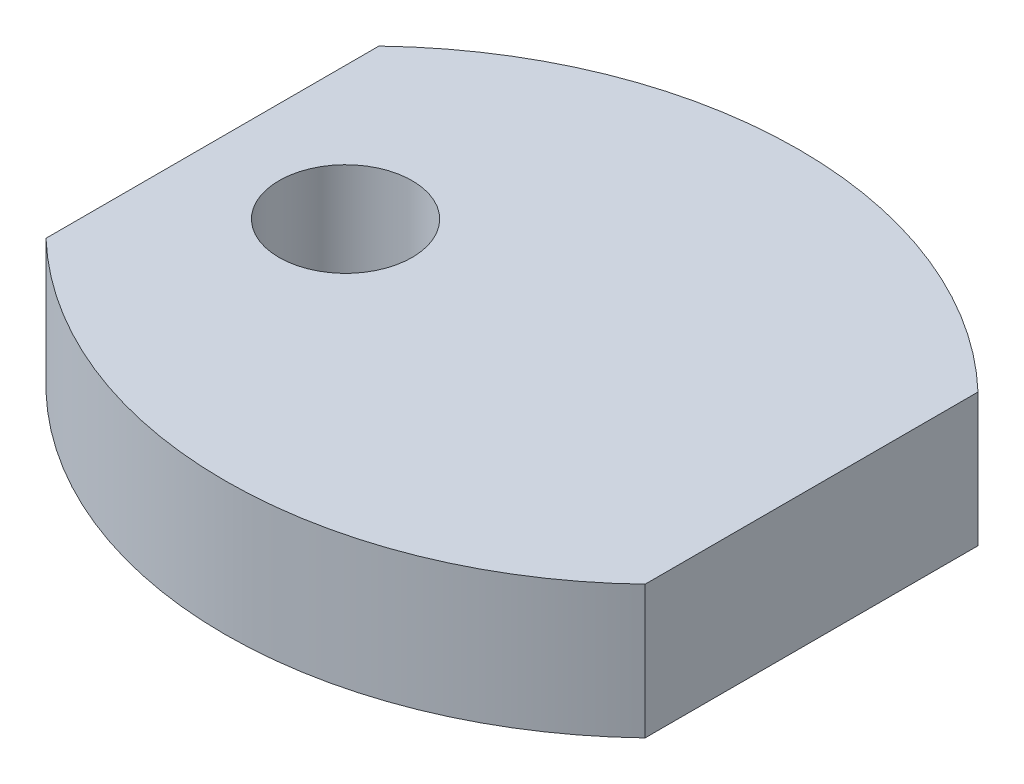
SolidWorks part; units mm, degrees
ref_plane "Спереди" through (0, 0, 0) normal (0, 0, 1) x (1, 0, 0)
ref_plane "Сверху" through (0, 0, 0) normal (0, 1, 0) x (1, 0, 0)
ref_plane "Справа" through (0, 0, 0) normal (1, 0, 0) x (0, 0, -1)
sketch "Sketch1" plane through (0, 0, 0) normal (0, 1, 0) x (1, 0, 0)
  line L0 (-9, 0) -> (9, 0) construction
  line L1 (9, -5) -> (-9, -5) construction
  line L2 (9, -5) -> (9, 5)
  line L3 (9, 5) -> (-9, 5) construction
  line L4 (-9, -5) -> (-9, 5)
  line L5 (9, -5) -> (-9, 5) construction
  line L6 (9, 5) -> (-9, -5) construction
  circle A0 centre (-5, 0) radius 2
  arc A1 (9, -5) -> (-9, -5) centre (0, 4.3808) cw
  arc A2 (9, 5) -> (-9, 5) centre (0, -4.3808) ccw
  point P0 (0, 0)
  dimension "D3" = 4
  dimension "D5" = 13
  dimension "D1" = 10
  dimension "D2" = 18
  dimension "D4" = 4
extrude "Boss-Extrude1" add sketch "Sketch1" along normal blind 4
